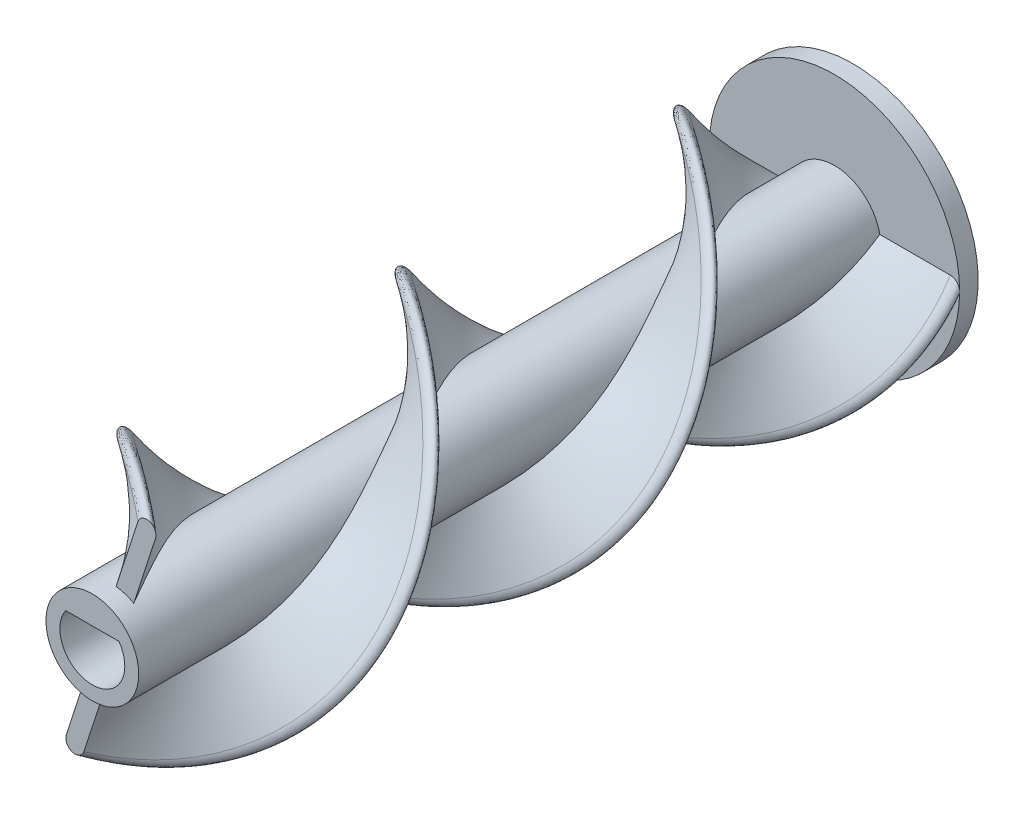
SolidWorks part; units mm, degrees
ref_plane "Front Plane" through (0, 0, 0) normal (0, 0, 1) x (1, 0, 0)
ref_plane "Top Plane" through (0, 0, 0) normal (0, 1, 0) x (1, 0, 0)
ref_plane "Right Plane" through (0, 0, 0) normal (1, 0, 0) x (0, 0, -1)
sketch "Sketch1" plane through (0, 0, 0) normal (0, 0, 1) x (1, 0, 0)
  circle A0 centre (0, 0) radius 5
  dimension "D1" = 10
extrude "Boss-Extrude1" add sketch "Sketch1" along normal blind 80
sketch "Sketch2" plane through (0, 0, 0) normal (0, 0, 1) x (1, 0, 0)
  line L0 (-12.5, 0) -> (12.5, 0) construction
  line L1 (-12.5, 1) -> (12.5, 1)
  line L2 (-12.5, -1) -> (12.5, -1)
  arc A0 (-12.5, 1) -> (-12.5, -1) centre (-12.5, 0) ccw
  arc A1 (12.5, -1) -> (12.5, 1) centre (12.5, 0) ccw
  point P2 (0, 0)
  dimension "D2" = 1
  dimension "D1" = 25
sketch "Sketch3" plane through (0, 0, 0) normal (0, 0, 1) x (1, 0, 0)
  circle A0 centre (0, 0) radius 13.5
  arc A1 (12.5, -1) -> (12.5, 1) centre (12.5, 0) ccw construction
curve "Helix/Spiral1" pitch 60 height 78 turns 1.3
sweep "Sweep1" add profiles "Sketch2" path "Helix/Spiral1"
sketch "Sketch5" plane through (0, 0, 0) normal (0, 0, -1) x (-1, 0, 0)
  circle A0 centre (0, 0) radius 13.5
  dimension "D1" = 27
extrude "Boss-Extrude2" add sketch "Sketch5" along normal blind 2
sketch "Sketch4" plane through (0, 0, 80) normal (0, 0, 1) x (1, 0, 0)
  line L0 (-2.8723, 2) -> (2.8723, 2)
  arc A0 (-2.8723, 2) -> (2.8723, 2) centre (0, 0) ccw
  dimension "D1" = 7
  dimension "D2" = 2
extrude "Cut-Extrude1" cut sketch "Sketch4" against normal through all
